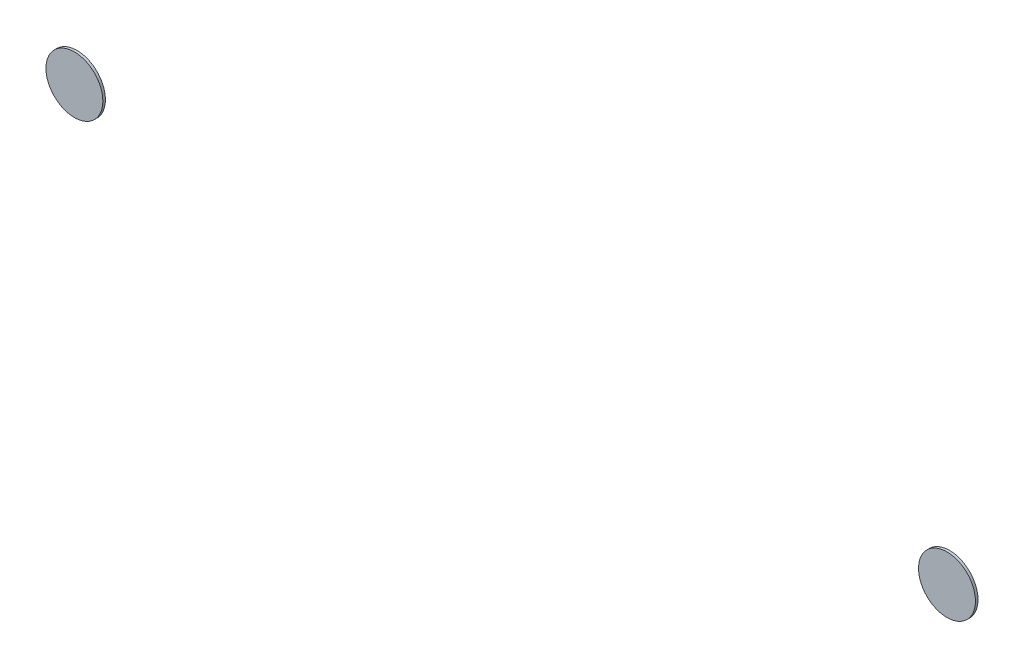
SolidWorks part; units mm, degrees
ref_plane "Alzado" through (0, 0, 0) normal (0, 0, 1) x (1, 0, 0)
ref_plane "Planta" through (0, 0, 0) normal (0, 1, 0) x (1, 0, 0)
ref_plane "Vista lateral" through (0, 0, 0) normal (1, 0, 0) x (0, 0, -1)
sketch "Model" plane through (0, 0, 0) normal (0, 0, 1) x (1, 0, 0)
  circle A0 centre (39.2523, 19.7639) radius 1.1055
  circle A1 centre (5.3477, 19.6361) radius 1.1055
extrude "Saliente-Extruir1" add sketch "Model" along normal blind 0.1
